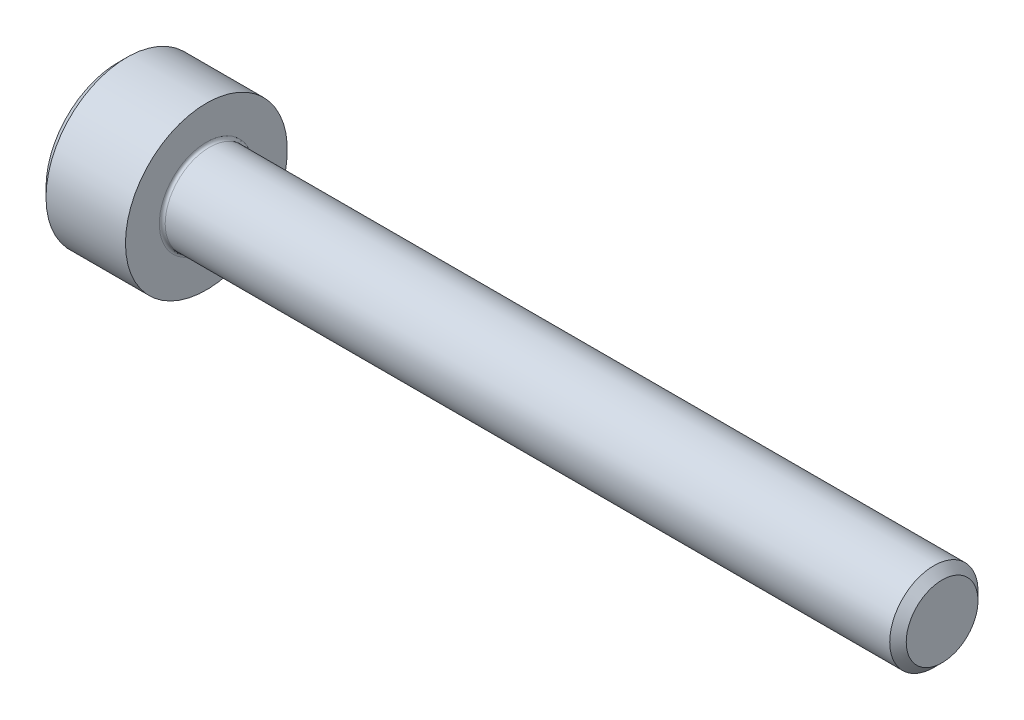
SolidWorks part; units mm, degrees
revolve "Base-Revolve" add sketch "BodySke"
sketch "BodySke" plane through (0, 0, 0) normal (0, 0, 1) x (1, 0, 0)
  line L0 (0, 0) -> (0, 2.45)
  line L1 (0.3, 2.75) -> (3, 2.75)
  line L2 (3, 2.75) -> (3, 1.5)
  line L3 (3, 1.5) -> (27.7195, 1.5)
  line L4 (28, 1.2195) -> (28, 0)
  line L5 (28, 0) -> (0, 0)
  line L6 (-31.75, 0) -> (127, 0) construction
  line L7 (0, 2.45) -> (0.3, 2.75)
  line L8 (28, 1.2195) -> (27.7195, 1.5)
  line L9 (0, -2.45) -> (0.3, -2.75) construction
  line L10 (28, -1.2195) -> (27.7195, -1.5) construction
  line L11 (3.5, 9.525) -> (3.5, 3.175) construction
  line L12 (10, 9.525) -> (10, 3.175) construction
  line L13 (-22, 9.525) -> (-22, 3.175) construction
  dimension "Diameter" = 3
  dimension "Head_ht" = 3
  dimension "Length" = 25
  dimension "Body_ch_ang" = 45
  dimension "Head_dia" = 5.5
  dimension "Head_ch_ang" = 45
  dimension "Minor_dia" = 2.439
  dimension "Advance" = 0.5
  dimension "Thread_nom" = 18
  dimension "Thread_length" = 50
  dimension "Head_ch_ht" = 0.3
cosmetic thread "ThreadCosmetic" [suppressed]
fillet "Fillet1" radius 0.1 1 edges at (3, 0, 1.5)
ref_plane "Plane1" through (0, 0, 0) normal (0, 0, 1) x (1, 0, 0)
ref_plane "Plane2" through (0, 0, 0) normal (0, 1, 0) x (1, 0, 0)
ref_plane "Plane3" through (0, 0, 0) normal (1, 0, 0) x (0, 0, -1)
sketch "Sketch2" plane through (0, 0, 0) normal (0, 0, 1) x (1, 0, 0)
  line L0 (0, 1.28) -> (1.3, 1.28)
  line L1 (1.3, 1.28) -> (2.039, 0)
  line L2 (-31.75, 0) -> (127, 0) construction
  line L3 (2.039, 0) -> (0, 0)
  line L4 (0, 0) -> (0, 1.28)
  line L5 (0, 2.45) -> (0, -2.45) construction
  line L6 (0, 0) -> (47.625, 0) construction
  line L7 (3, -2.75) -> (3, 2.75) construction
  dimension "D1" = 1.28
  dimension "D2" = 60
revolve "Hex-PreBroach" cut sketch "Sketch2" angle 360 about L6
sketch "Sketch3" plane through (0, 0, 0) normal (-1, 0, 0) x (0, 0.5, 0.866)
  line L0 (0.739, 1.28) -> (-0.739, 1.28)
  line L1 (-0.739, 1.28) -> (-1.478, 0)
  line L2 (0.739, 1.28) -> (1.478, 0)
  line L3 (0.739, -1.28) -> (1.478, 0)
  line L4 (0.739, -1.28) -> (-0.739, -1.28)
  line L5 (-0.739, -1.28) -> (-1.478, 0)
  dimension "D1" = 1.28
  dimension "D2" = 1.28
  dimension "Hex_size" = 2.56
extrude "Hex" cut sketch "Sketch3" against normal blind 1.3
sketch "Sketch4" plane through (0, 0, 0) normal (-1, 0, 0) x (0, 0, 1)
  line L0 (0, 0) -> (1.4605, 0)
  line L1 (0, 0) -> (6.1484, 3.5498) construction
  line L2 (0, 0) -> (0.7302, 1.2648)
  line L3 (1.2009, 0.3267) -> (1.3933, 0.4378)
  line L4 (0.8834, 0.8767) -> (1.0758, 0.9877)
  arc A0 (1.2009, 0.3267) -> (0.8834, 0.8767) centre (0, 0) ccw
  arc A1 (1.4605, 0) -> (1.3933, 0.4378) centre (0, 0) ccw
  arc A2 (0.7302, 1.2648) -> (1.0758, 0.9877) centre (0, 0) cw
  dimension "D1" = 30
  dimension "D2" = 60
  dimension "Spline_p_dim" = 0.635
  dimension "D3" = 0.3175
extrude "Spline" [suppressed] cut sketch "Sketch4" against normal blind 1.3
pattern_circular "CirPattern1" [suppressed] count 6 every 60
sketch "Sketch5" plane through (0, 0, 0) normal (0, 0, 1) x (1, 0, 0)
  line L0 (-31.75, 0) -> (127, 0) construction
  line L2 (0, 2.45) -> (0, -2.45) construction
  circle A0 centre (1.2, 0) radius 0.475
  dimension "Drilled_hole_dia" = 0.95
  dimension "Drilled_hole_loc" = 1.2
extrude "Hole" [suppressed] cut sketch "Sketch5" against normal through all and the other way through all
pattern_circular "Drilled-4" [suppressed] count 2 every 60
pattern_circular "Drilled-6" [suppressed] count 3 every 60
sketch "ThdSchSke" plane through (0, 0, 0) normal (0, 0, 1) x (1, 0, 0)
  line L0 (10, -1.2195) -> (9.8036, -1.5)
  line L1 (10, -1.2195) -> (10.1964, -1.5)
  line L2 (10.1964, -1.5) -> (10.1964, -1.875)
  line L3 (-3.175, 0) -> (5.1513, 0) construction
  line L5 (10.1964, -1.875) -> (9.8036, -1.875)
  line L6 (9.8036, -1.875) -> (9.8036, -1.5)
  line L7 (0, 2.45) -> (0, -2.45) construction
  dimension "Thread_minor" = 2.439
  dimension "Diameter" = 3
  dimension "Start" = 10
revolve "ThreadSchematic" [suppressed] cut sketch "ThdSchSke" angle 360 about L3
pattern_linear "ThdSchPat" [suppressed]
equation "\"D2@Sketch3\" = \"Hex_size@Sketch3\" / 2"
equation "\"D1@Sketch3\" = \"Hex_size@Sketch3\" / 2"
equation "\"D1@Sketch2\" = \"Hex_size@Sketch3\" / 2"
equation "\"D3@Sketch4\" = \"Spline_p_dim@Sketch4\" / 2"
equation "\"Thread_minor@ThreadCosmetic\"  =  \"Minor_dia@BodySke\""
equation "\"D2@CirPattern1\" = 360 / \"Num_teeth@CirPattern1\""
equation "\"Wall_thickness@Sketch2\" = \"Head_ht@BodySke\" - \"Key_eng@Hex\""
equation "\"Thread_length@ThreadCosmetic\" = ((sgn( (\"Length@BodySke\" - \"Advance@BodySke\" ) - \"Thread_nom@BodySke\" )-1)*( (\"Length@BodySke\" - \"Advance@BodySke\" ) - \"Thread_nom@BodySke\" ))/-2+ \"Thread_nom@BodySke\""
equation "\"Thread_minor@ThdSchSke\" = \"Minor_dia@BodySke\""
equation "\"Diameter@ThdSchSke\" = \"Diameter@BodySke\""
equation "\"Overcut@ThdSchSke\" = \"Diameter@BodySke\" * 1.25"
equation "\"Start@ThdSchSke\" = \"Head_ht@BodySke\" + \"Length@BodySke\" - \"Thread_length@ThreadCosmetic\"  '---Non-countersunk---"
equation "\"Num_threads@ThdSchPat\" = int( \"Thread_length@ThreadCosmetic\" / \"Advance@BodySke\" + 0.999 )  + 1"
equation "\"Advance@ThdSchPat\" = \"Thread_length@ThreadCosmetic\" /  (\"Num_threads@ThdSchPat\" - 1) 'relax it"
equation "\"Num_threads@ThdSchPat\" = \"Num_threads@ThdSchPat\" - sgn( \"Num_threads@ThdSchPat\" - 1) '---chamfered tips only---"
